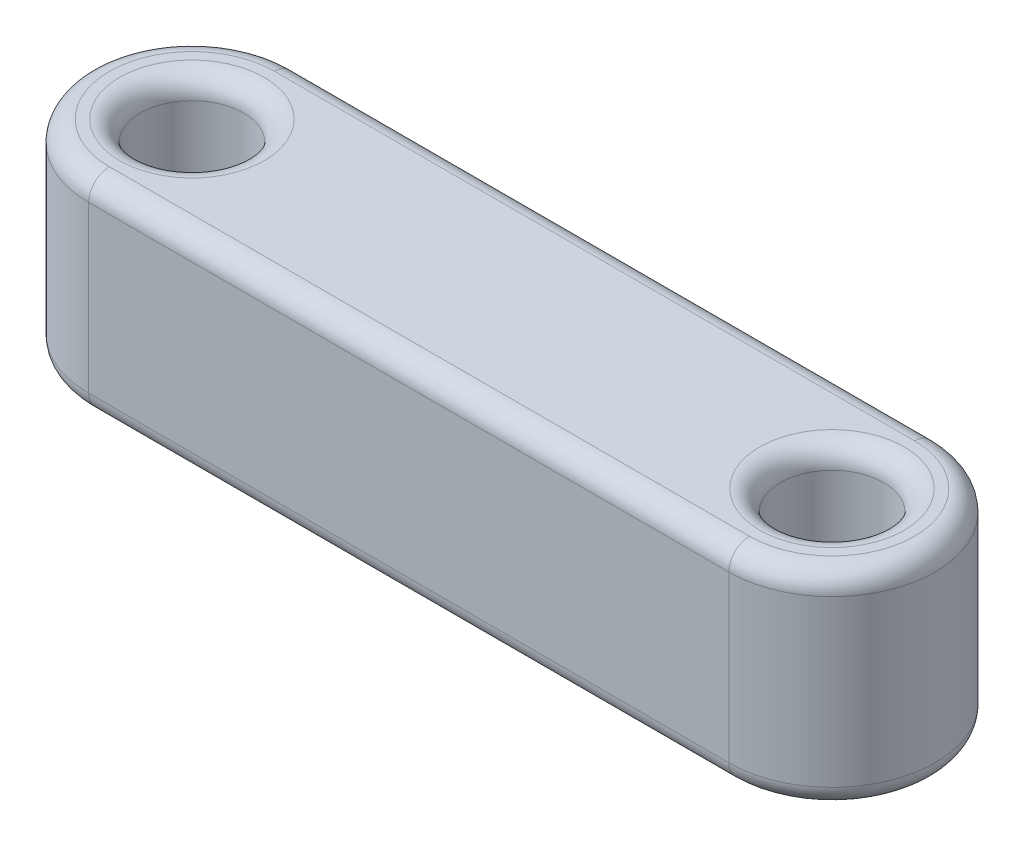
SolidWorks part; units mm, degrees
ref_plane "Front Plane" through (0, 0, 0) normal (0, 0, 1) x (1, 0, 0)
ref_plane "Top Plane" through (0, 0, 0) normal (0, 1, 0) x (1, 0, 0)
ref_plane "Right Plane" through (0, 0, 0) normal (1, 0, 0) x (0, 0, -1)
sketch "Sketch1" plane through (0, 0, 0) normal (0, 1, 0) x (1, 0, 0)
  line L0 (0, 0) -> (31, 0) construction
  line L1 (0, 5) -> (31, 5)
  line L2 (0, -5) -> (31, -5)
  arc A0 (0, 5) -> (0, -5) centre (0, 0) ccw
  arc A1 (31, -5) -> (31, 5) centre (31, 0) ccw
  circle A2 centre (0, 0) radius 2.5
  circle A3 centre (31, 0) radius 2.5
  point P3 (15.5, 0)
  dimension "D1" = 5
  dimension "D3" = 5
  dimension "D4" = 5
  dimension "D2" = 31
extrude "Boss-Extrude1" add sketch "Sketch1" along normal blind 10
fillet "Fillet1" radius 1 12 edges at (31, 0, 2.5) (0, 0, 2.5) (15.5, 0, 5) (36, 0, 0) (15.5, 0, -5) (-5, 0, 0) (31, 10, 2.5) (15.5, 10, -5) (36, 10, 0) (15.5, 10, 5) (-5, 10, 0) (0, 10, 2.5)
